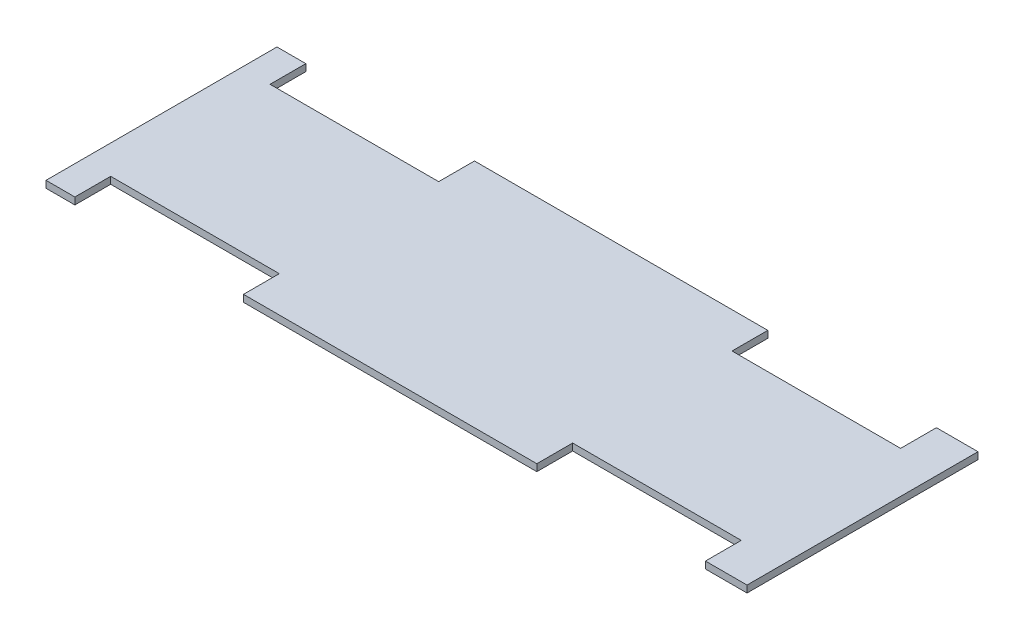
SolidWorks part; units mm, degrees
ref_plane "Front Plane" through (0, 0, 0) normal (0, 0, 1) x (1, 0, 0)
ref_plane "Top Plane" through (0, 0, 0) normal (0, 1, 0) x (1, 0, 0)
ref_plane "Right Plane" through (0, 0, 0) normal (1, 0, 0) x (0, 0, -1)
sketch "Sketch1" plane through (0, 0, 0) normal (0, 1, 0) x (1, 0, 0)
  line L0 (-149, -50) -> (-149, 50)
  line L1 (-149, 50) -> (-136.5, 50)
  line L2 (-136.5, 50) -> (-136.5, 34.5)
  line L3 (-136.5, 34.5) -> (-63.5, 34.5)
  line L4 (-63.5, 34.5) -> (-63.5, 50)
  line L5 (-63.5, 50) -> (63.5, 50)
  line L6 (63.5, 50) -> (63.5, 34.5)
  line L7 (63.5, 34.5) -> (136.5, 34.5)
  line L8 (136.5, 34.5) -> (136.5, 50)
  line L9 (136.5, 50) -> (154.5, 50)
  line L10 (154.5, 50) -> (154.5, -50)
  line L11 (154.5, -50) -> (136.5, -50)
  line L12 (136.5, -50) -> (136.5, -34.5)
  line L13 (136.5, -34.5) -> (63.5, -34.5)
  line L14 (63.5, -34.5) -> (63.5, -50)
  line L15 (63.5, -50) -> (-63.5, -50)
  line L16 (-63.5, -50) -> (-63.5, -34.5)
  line L17 (-63.5, -34.5) -> (-136.5, -34.5)
  line L18 (-136.5, -34.5) -> (-136.5, -50)
  line L19 (-136.5, -50) -> (-149, -50)
  point P18 (0, 50)
  point P21 (-149, 0)
  dimension "D1" = 100
  dimension "D2" = 69
  dimension "D3" = 73
  dimension "D4" = 12.5
  dimension "D5" = 127
  dimension "D6" = 73
  dimension "D7" = 18
extrude "Boss-Extrude1" add sketch "Sketch1" along normal blind 3
